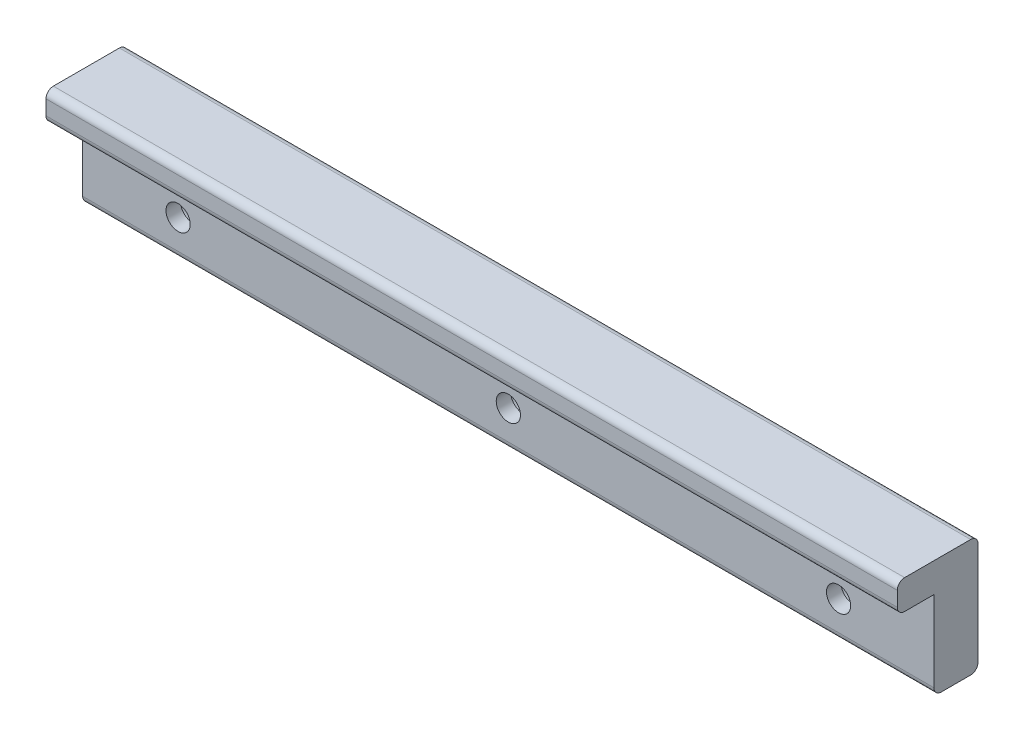
SolidWorks part; units mm, degrees
ref_plane "Front Plane" through (0, 0, 0) normal (0, 0, 1) x (1, 0, 0)
ref_plane "Top Plane" through (0, 0, 0) normal (0, 1, 0) x (1, 0, 0)
ref_plane "Right Plane" through (0, 0, 0) normal (1, 0, 0) x (0, 0, -1)
sketch "Sketch2" plane through (0, 0, 0) normal (1, 0, 0) x (0, 0, -1)
  line L0 (0, 0) -> (0, 12)
  line L1 (0, 12) -> (-5, 12)
  line L2 (-5, 12) -> (-5, 16)
  line L3 (-5, 16) -> (6, 16)
  line L4 (6, 16) -> (6, 0)
  line L5 (6, 0) -> (0, 0)
  dimension "D1" = 6
  dimension "D2" = 12
  dimension "D3" = 5
  dimension "D4" = 4
extrude "Boss-Extrude1" add sketch "Sketch2" along normal blind 116
sketch "Sketch3" plane through (0, 0, -6) normal (0, 0, -1) x (-1, 0, 0)
  line L0 (-116, 5) -> (0, 5) construction
  line L1 (-116, 0) -> (-116, 16) construction
  line L2 (0, 0) -> (0, 16) construction
  line L4 (-116, 12) -> (-98.0092, 12) construction
  line L5 (-98.0092, 12) -> (-98.0092, 16) construction
  line L6 (-116, 16) -> (0, 16) construction
  circle A0 centre (-103, 5) radius 1.65
  circle A1 centre (-13, 5) radius 1.65
  circle A2 centre (-58, 5) radius 1.65
  dimension "D3" = 3.3
  dimension "D1" = 45
  dimension "D2" = 45
  dimension "D4" = 4
  dimension "D5" = 7
extrude "Cut-Extrude1" cut sketch "Sketch3" against normal up to next
sketch "Sketch4" plane through (0, 0, -6) normal (0, 0, -1) x (-1, 0, 0)
  circle A0 centre (-103, 5) radius 3
  circle A1 centre (-58, 5) radius 3
  circle A2 centre (-13, 5) radius 3
  dimension "D1" = 6
extrude "Cut-Extrude2" cut sketch "Sketch4" against normal blind 4
fillet "Fillet1" radius 1 5 edges at (58, 0, -6) (58, 16, -6) (58, 16, 5) (58, 12, 5) (58, 0, 0)
